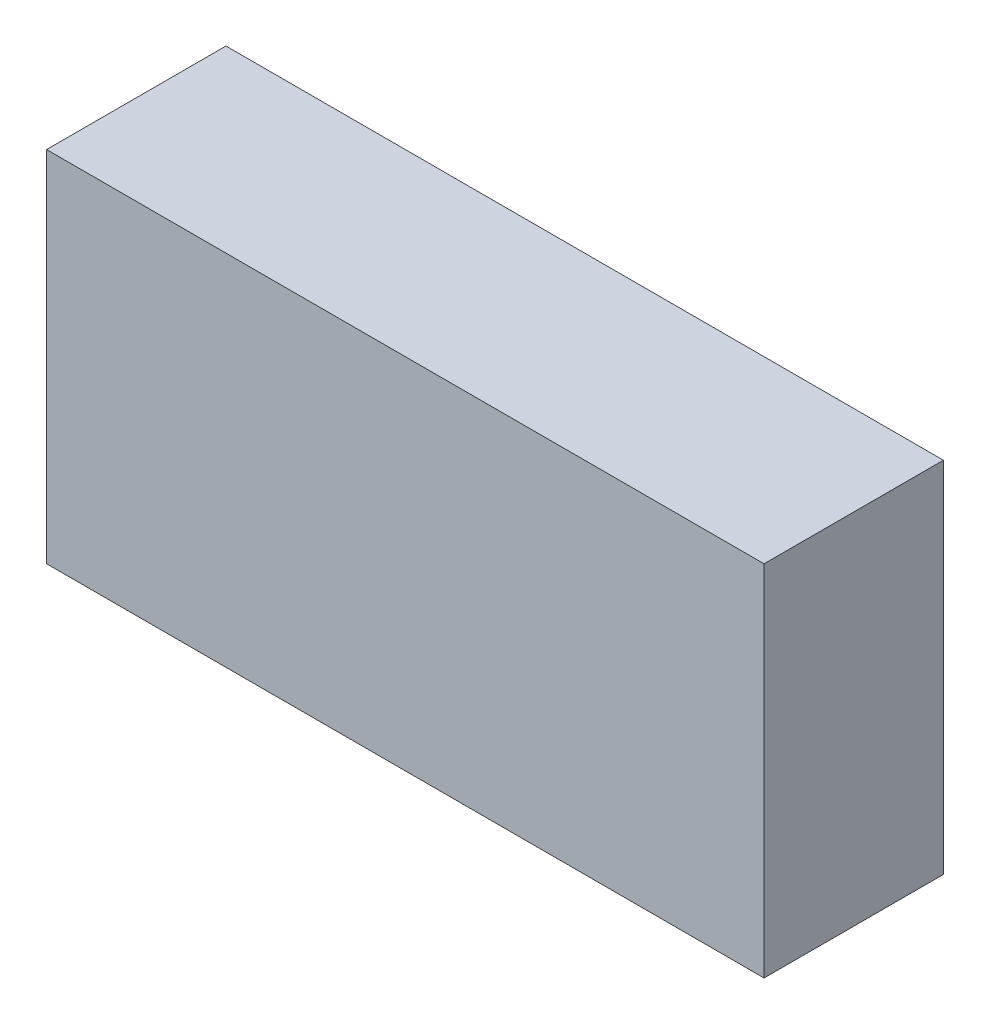
SolidWorks part; units mm, degrees
ref_plane "Płaszczyzna przednia" through (0, 0, 0) normal (0, 0, 1) x (1, 0, 0)
ref_plane "Płaszczyzna górna" through (0, 0, 0) normal (0, 1, 0) x (1, 0, 0)
ref_plane "Płaszczyzna prawa" through (0, 0, 0) normal (1, 0, 0) x (0, 0, -1)
sketch "Szkic1" plane through (0, 0, 0) normal (0, 0, 1) x (1, 0, 0)
  line L1 (0, 0) -> (20, 0)
  line L2 (0, 0) -> (0, 10)
  line L3 (0, 10) -> (20, 10)
  line L4 (20, 0) -> (20, 10)
  dimension "D1" = 20
  dimension "D2" = 10
extrude "Dodanie-wyciągnięcie1" add sketch "Szkic1" along normal blind 5
